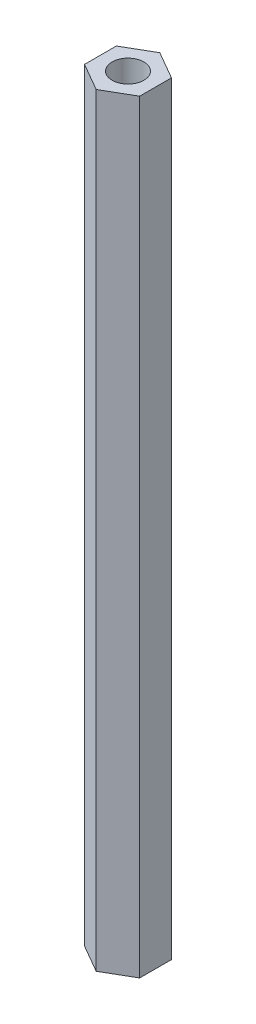
SolidWorks part; units mm, degrees
ref_plane "Face" through (0, 0, 0) normal (0, 0, 1) x (1, 0, 0)
ref_plane "Dessus" through (0, 0, 0) normal (0, 1, 0) x (1, 0, 0)
ref_plane "Droite" through (0, 0, 0) normal (1, 0, 0) x (0, 0, -1)
sketch "Esquisse1" plane through (0, 0, 0) normal (0, 1, 0) x (1, 0, 0)
  line L0 (0, 0) -> (0, 5.5688) construction
  line L1 (0, 5) -> (-4.3301, 2.5)
  line L2 (-4.3301, 2.5) -> (-4.3301, -2.5)
  line L3 (-4.3301, -2.5) -> (0, -5)
  line L4 (0, -5) -> (4.3301, -2.5)
  line L5 (4.3301, -2.5) -> (4.3301, 2.5)
  line L6 (4.3301, 2.5) -> (0, 5)
  circle A0 centre (0, 0) radius 4.3301 construction
  circle A1 centre (0, 0) radius 2.5
  dimension "D1" = 10
  dimension "D2" = 5
extrude "Extrusion1" add sketch "Esquisse1" along normal blind 120
